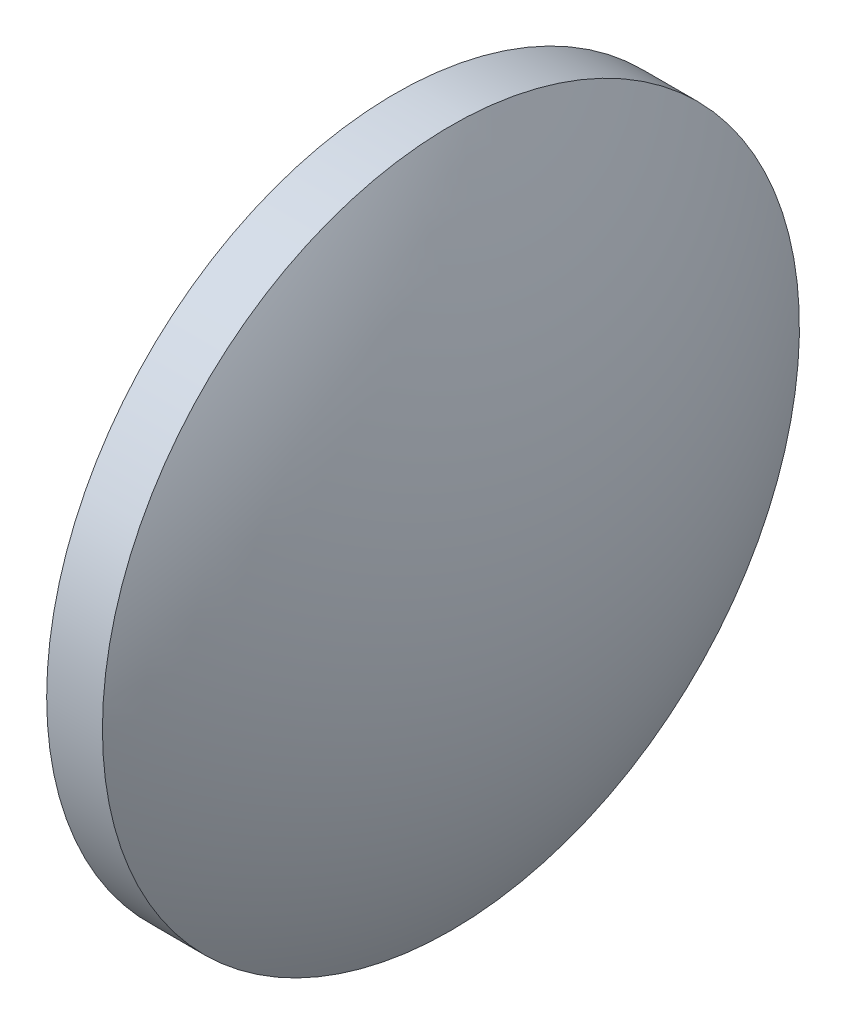
SolidWorks part; units mm, degrees
ref_plane "前视基准面" through (0, 0, 0) normal (0, 0, 1) x (1, 0, 0)
ref_plane "上视基准面" through (0, 0, 0) normal (0, 1, 0) x (1, 0, 0)
ref_plane "右视基准面" through (0, 0, 0) normal (1, 0, 0) x (0, 0, -1)
sketch "草图1" plane through (0, 0, 0) normal (0, 0, 1) x (1, 0, 0)
  line L0 (462.7413, 58.1679) -> (472.1393, 58.1679) construction
  line L1 (465.5821, 58.1679) -> (465.5821, 65.6679)
  line L2 (465.5821, 65.6679) -> (466.7821, 65.6679)
  line L3 (468.7821, 58.1679) -> (465.5821, 58.1679)
  arc A0 (468.7821, 58.1679) -> (466.7821, 65.6679) centre (453.7196, 58.1679) ccw
revolve "旋转1" add sketch "草图1" angle 360 about L0
